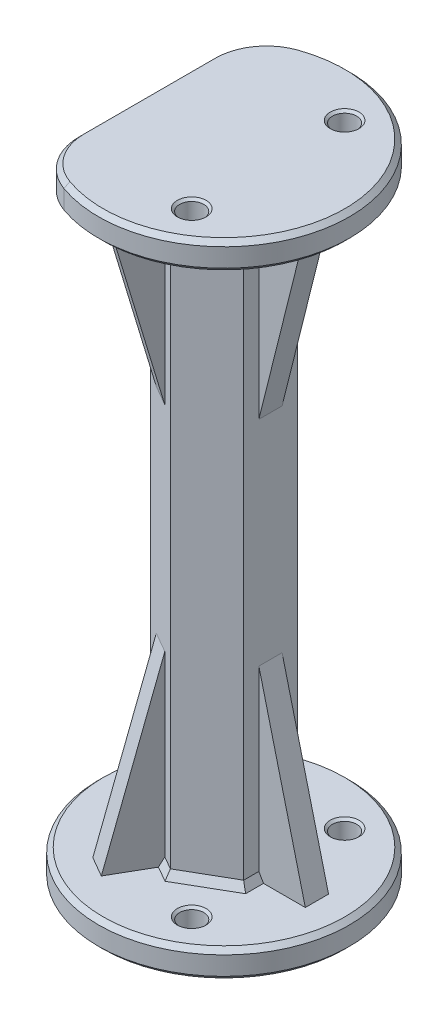
SolidWorks part; units mm, degrees
material "PET"
ref_plane "Front Plane" through (0, 0, 0) normal (0, 0, 1) x (1, 0, 0)
ref_plane "Top Plane" through (0, 0, 0) normal (0, 1, 0) x (1, 0, 0)
ref_plane "Right Plane" through (0, 0, 0) normal (1, 0, 0) x (0, 0, -1)
sketch "Sketch3" plane through (0, 0, 0) normal (0, 1, 0) x (1, 0, 0)
  circle A0 centre (0, 0) radius 27
  dimension "D1" = 54
extrude "Boss-Extrude1" add sketch "Sketch3" along normal blind 6
sketch "Sketch4" plane through (0, 6, 0) normal (0, 1, 0) x (1, 0, 0)
  line L0 (0, 0) -> (0, 11.547) construction
  line L1 (10, -5.7735) -> (10, 5.7735)
  line L2 (10, 5.7735) -> (0, 11.547)
  line L3 (0, 11.547) -> (-10, 5.7735)
  line L4 (-10, 5.7735) -> (-10, -5.7735)
  line L5 (-10, -5.7735) -> (0, -11.547)
  line L6 (0, -11.547) -> (10, -5.7735)
  circle A0 centre (0, 0) radius 10 construction
  dimension "D1" = 20
extrude "Boss-Extrude2" add sketch "Sketch4" along normal blind 126
sketch "Sketch19" plane through (0, 132, 0) normal (0, 1, 0) x (1, 0, 0)
  circle A0 centre (0, 0) radius 27 construction
  circle A1 centre (0, 0) radius 27
extrude "Boss-Extrude3" add sketch "Sketch19" along normal blind 6
sketch "Sketch13" plane through (0, 6, 0) normal (0, 1, 0) x (1, 0, 0)
  line L0 (-19, 0) -> (0, 0) construction
  line L1 (-19, 0) -> (9.5, 16.4545) construction
  line L2 (9.5, 16.4545) -> (9.5, -16.4545) construction
  line L3 (9.5, -16.4545) -> (-19, 0) construction
  circle A0 centre (-19, 0) radius 2.6
  circle A1 centre (0, 0) radius 19 construction
  circle A2 centre (9.5, 16.4545) radius 2.6
  circle A3 centre (9.5, -16.4545) radius 2.6
  point P12 (0, 0)
  dimension "D2" = 38
  dimension "D3" = 5.2
  dimension "D1" = 3
extrude "Cut-Extrude5" cut sketch "Sketch13" against normal up to next
sketch "Sketch20" plane through (0, 138, 0) normal (0, 1, 0) x (1, 0, 0)
  circle A0 centre (9.5, 16.4545) radius 2.6 construction
  circle A1 centre (9.5, -16.4545) radius 2.6 construction
  circle A2 centre (9.5, 16.4545) radius 2.6
  circle A3 centre (9.5, -16.4545) radius 2.6
extrude "Cut-Extrude6" cut sketch "Sketch20" against normal up to next
sketch "Sketch21" plane through (0, 138, 0) normal (0, 1, 0) x (1, 0, 0)
  line L1 (-17, 20.9762) -> (-27, 20.9762)
  line L2 (-17, 20.9762) -> (-17, -20.9762)
  line L3 (-17, -20.9762) -> (-27, -20.9762)
  line L4 (-27, 20.9762) -> (-27, -20.9762)
  circle A0 centre (0, 0) radius 27 construction
  dimension "D1" = 10
extrude "Cut-Extrude7" cut sketch "Sketch21" against normal up to next
ref_plane "Plane1" through (0, 69, 0) normal (0, 1, 0) x (1, 0, 0)
sketch "Sketch18" plane through (0, 0, 0) normal (0, 0, 1) x (1, 0, 0)
  line L0 (10, 46) -> (20, 6)
  line L1 (20, 6) -> (10, 6) construction
  line L2 (10, 6) -> (10, 46) construction
  line L3 (-16.4, 6) -> (-21.6, 6) construction
  line L4 (10, 132) -> (10, 6) construction
  dimension "D1" = 20
  dimension "D2" = 40
rib "Rib3" sketch "Sketch18" sketch "Sketch18" thickness 5 extrusion direction parallel to sketch draft on no parameters "D1"=5
pattern_circular "CirPattern1" count 3 over 360 about axis through (0, 0, 0) along (0, 1, 0) of "Rib3"
mirror "Mirror2" about plane through (0, 69, 0) normal (0, 1, 0) of "CirPattern1", "Rib3"
fillet "Fillet1" radius 12 2 edges at (-17, 135, -20.9762) (-17, 135, 20.9762)
chamfer "Chamfer1" distance 1 angle 60 18 edges at (-1.4175, 6, -10.7286) (-8.5825, 6, -6.5919) (-10, 6, 0) (5, 6, -8.6603) (10, 6, 4.1368) (10, 6, -4.1368) (-8.5825, 6, 6.5919) (-1.4175, 6, 10.7286) (5, 6, 8.6603) (-1.4175, 132, -10.7286) (-8.5825, 132, -6.5919) (-10, 132, 0) (-8.5825, 132, 6.5919) (-1.4175, 132, 10.7286) (5, 132, 8.6603) (10, 132, 4.1368) (10, 132, -4.1368) (5, 132, -8.6603)
chamfer "Chamfer2" distance 1 angle 45 10 edges at (0, 0, 27) (0, 6, 27) (27, 138, 0) (27, 132, 0) (-17, 138, 0) (-14.798, 138, 21.0703) (-14.798, 138, -21.0703) (-17, 132, 0) (-14.798, 132, 21.0703) (-14.798, 132, -21.0703)
chamfer "Chamfer3" distance 0.5 angle 45 10 edges at (9.5, 0, 19.0545) (-19, 0, 2.6) (9.5, 0, -13.8545) (9.5, 6, -13.8545) (9.5, 6, 19.0545) (-19, 6, 2.6) (9.5, 132, 19.0545) (9.5, 138, 19.0545) (9.5, 132, -13.8545) (9.5, 138, -13.8545)
